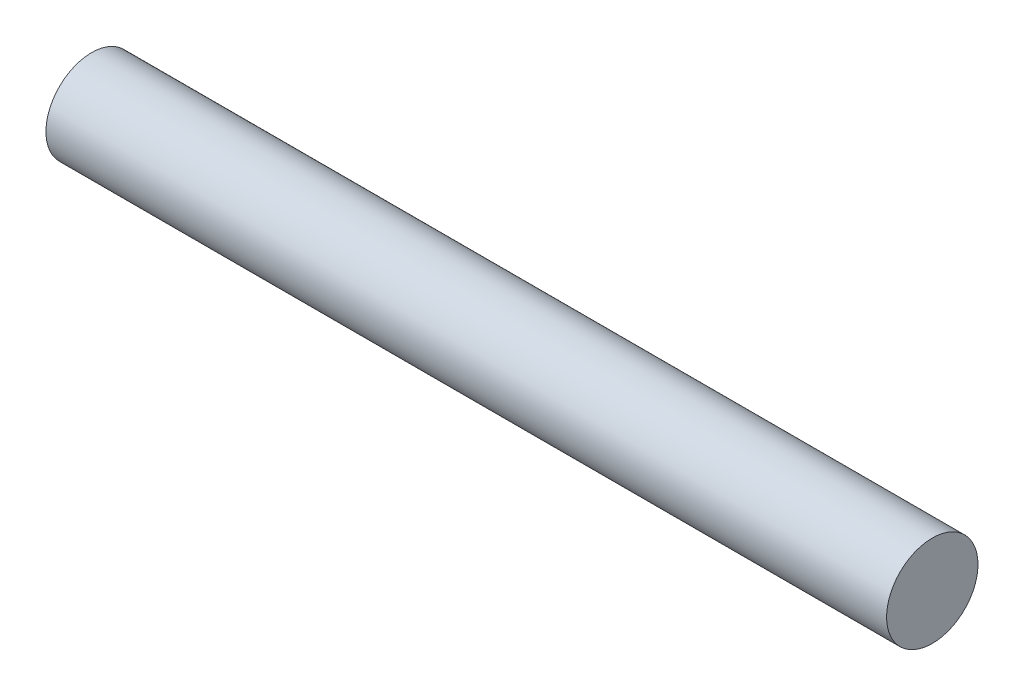
SolidWorks part; units mm, degrees
ref_plane "Front Plane" through (0, 0, 0) normal (0, 0, 1) x (1, 0, 0)
ref_plane "Top Plane" through (0, 0, 0) normal (0, 1, 0) x (1, 0, 0)
ref_plane "Right Plane" through (0, 0, 0) normal (1, 0, 0) x (0, 0, -1)
sketch "Sketch1" plane through (0, 0, 0) normal (1, 0, 0) x (0, 0, -1)
  circle A0 centre (0, 0) radius 1.25
extrude "Boss-Extrude1" add sketch "Sketch1" along normal blind 23
